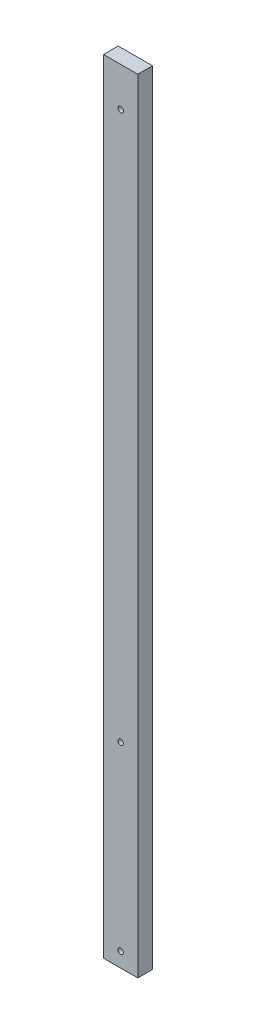
SolidWorks part; units mm, degrees
material "Oak"
ref_plane "Front Plane" through (0, 0, 0) normal (0, 0, 1) x (1, 0, 0)
ref_plane "Top Plane" through (0, 0, 0) normal (0, 1, 0) x (1, 0, 0)
ref_plane "Right Plane" through (0, 0, 0) normal (1, 0, 0) x (0, 0, -1)
sketch "Sketch1" plane through (0, 0, 0) normal (0, 1, 0) x (1, 0, 0)
  line L1 (-44.45, -19.05) -> (44.45, -19.05)
  line L2 (-44.45, -19.05) -> (-44.45, 19.05)
  line L3 (-44.45, 19.05) -> (44.45, 19.05)
  line L4 (44.45, -19.05) -> (44.45, 19.05)
  line L5 (-44.45, -19.05) -> (44.45, 19.05) construction
  line L6 (-44.45, 19.05) -> (44.45, -19.05) construction
  point P0 (0, 0)
  dimension "D1" = 38.1
  dimension "D2" = 88.9
extrude "Boss-Extrude1" add sketch "Sketch1" along normal blind 2032 contours L3 L4 L1 L2
sketch "Sketch2" plane through (0, 0, 19.05) normal (0, 0, 1) x (1, 0, 0)
  line L0 (0, 2032) -> (0, 0) construction
  line L1 (-44.45, 2032) -> (44.45, 2032) construction
  line L2 (-44.45, 0) -> (44.45, 0) construction
  circle A0 centre (0, 38.1) radius 7.1438
  circle A1 centre (0, 508) radius 7.1437
  circle A2 centre (0, 1930.4) radius 7.1438
  dimension "D1" = 14.2875
  dimension "D2" = 38.1
  dimension "D3" = 508
  dimension "D4" = 1930.4
extrude "Cut-Extrude1" cut sketch "Sketch2" against normal through all both and the other way through all
